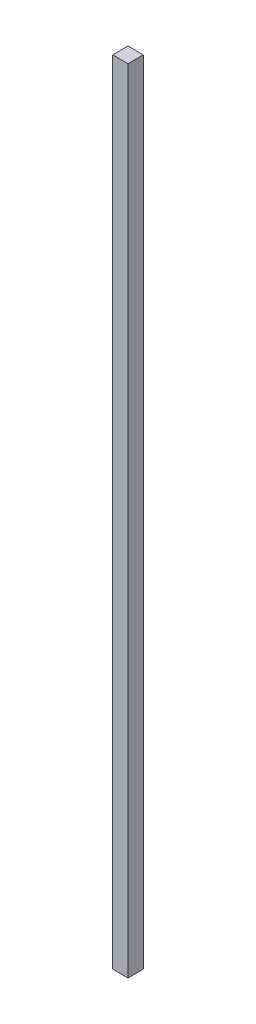
SolidWorks part; units mm, degrees
ref_plane "Plan de face" through (0, 0, 0) normal (0, 0, 1) x (1, 0, 0)
ref_plane "Plan de dessus" through (0, 0, 0) normal (0, 1, 0) x (1, 0, 0)
ref_plane "Plan de droite" through (0, 0, 0) normal (1, 0, 0) x (0, 0, -1)
sketch "Esquisse1" plane through (0, 0, 0) normal (0, 0, 1) x (1, 0, 0)
  line L1 (-20.484, 21.2185) -> (-10.484, 21.2185)
  line L2 (-20.484, 21.2185) -> (-20.484, -495.7815)
  line L3 (-20.484, -495.7815) -> (-10.484, -495.7815)
  line L4 (-10.484, 21.2185) -> (-10.484, -495.7815)
  dimension "D1" = 10
  dimension "D2" = 517
extrude "Boss.-Extru.1" add sketch "Esquisse1" along normal blind 10
equation "\"D2@Esquisse1\"=\"HauteurCoteGauche\" - 23"
equation "\"EpaisseurPlaque\"= 3"
equation "\"ProfondeurBoite\"=460"
equation "\"LongueurSyphon\"=270"
equation "\"LargeurSyphon\"=120"
equation "\"HauteurCoteDroit\"= 490"
equation "\"HauteurCoteGauche\"= 540"
equation "\"HauteurSolSyphon\"= 300"
equation "\"HauteurSyphon\"=\"HauteurCoteGauche\"-\"HauteurSolSyphon\""
equation "\"LargeurDroite\"=10"
equation "\"LargeurGauche\"=150"
equation "\"LargeurBoite\"= \"LargeurDroite\" + \"LargeurGauche\" + \"LargeurSyphon\""
